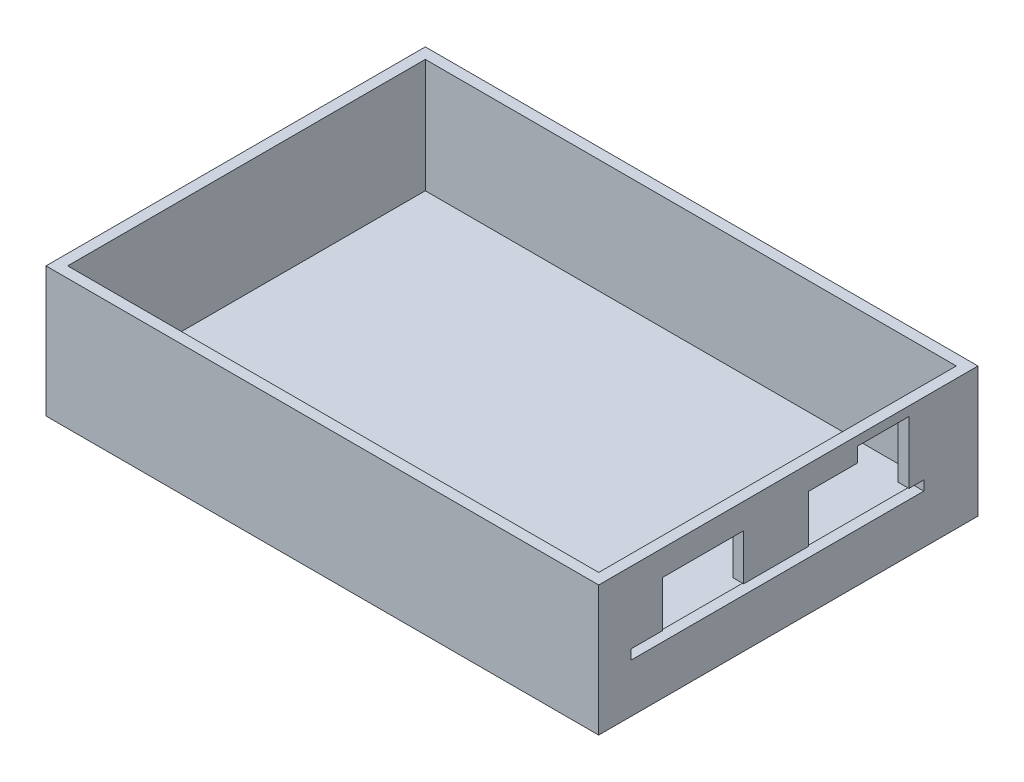
SolidWorks part; units mm, degrees
ref_plane "Alzado" through (0, 0, 0) normal (0, 0, 1) x (1, 0, 0)
ref_plane "Planta" through (0, 0, 0) normal (0, 1, 0) x (1, 0, 0)
ref_plane "Vista lateral" through (0, 0, 0) normal (1, 0, 0) x (0, 0, -1)
sketch "Croquis1" plane through (0, 0, 0) normal (0, 1, 0) x (1, 0, 0)
  line L1 (0, 0) -> (102, 0)
  line L2 (0, 0) -> (0, 70)
  line L3 (0, 70) -> (102, 70)
  line L4 (102, 0) -> (102, 70)
  dimension "D1" = 70
  dimension "D2" = 102
extrude "Saliente-Extruir1" add sketch "Croquis1" along normal blind 24
sketch "Croquis2" plane through (0, 24, 0) normal (0, 1, 0) x (1, 0, 0)
  line L0 (0, 70) -> (0, 0) construction
  line L1 (2, 2) -> (100, 2)
  line L2 (2, 2) -> (2, 68)
  line L3 (2, 68) -> (100, 68)
  line L4 (100, 2) -> (100, 68)
  line L5 (0, 0) -> (102, 0) construction
  line L6 (102, 0) -> (102, 70) construction
  line L7 (102, 70) -> (0, 70) construction
  dimension "D1" = 2
  dimension "D2" = 2
  dimension "D3" = 2
  dimension "D4" = 2
extrude "Cortar-Extruir1" cut sketch "Croquis2" against normal offset from surface (21 mm away) 3 up to face at (51, 0, -35)
sketch "Croquis3" plane through (102, 0, 0) normal (1, 0, 0) x (0, 0, -1)
  line L0 (0, 9) -> (70, 9) construction
  line L1 (0, 24) -> (0, 0) construction
  line L2 (70, 24) -> (70, 0) construction
  line L3 (0, 0) -> (70, 0) construction
  line L4 (6, 9) -> (60, 9)
  line L5 (60, 9) -> (60, 10.8)
  line L6 (60, 10.8) -> (57.25, 10.8)
  line L7 (57.25, 10.8) -> (57.25, 22.3)
  line L8 (57.25, 22.3) -> (47.75, 22.3)
  line L9 (47.75, 22.3) -> (47.75, 19.6)
  line L10 (47.75, 19.6) -> (38.75, 19.6)
  line L11 (38.75, 19.6) -> (38.75, 10.8)
  line L12 (38.75, 10.8) -> (26.75, 10.8)
  line L13 (26.75, 10.8) -> (26.75, 19.3)
  line L14 (26.75, 19.3) -> (11.75, 19.3)
  line L15 (11.75, 19.3) -> (11.75, 10.8)
  line L16 (11.75, 10.8) -> (6, 10.8)
  line L17 (6, 10.8) -> (6, 9)
  line L18 (38.75, 10.8) -> (38.75, 9) construction
  line L19 (26.75, 10.8) -> (26.75, 9) construction
  point P10 (0, 0)
  dimension "D1" = 9
  dimension "D2" = 1.8
  dimension "D3" = 11.5
  dimension "D4" = 2.75
  dimension "D5" = 10
  dimension "D6" = 9.5
  dimension "D7" = 2.7
  dimension "D8" = 9
  dimension "D9" = 8.5
  dimension "D10" = 15
  dimension "D11" = 54
  dimension "D12" = 12
extrude "Cortar-Extruir2" cut sketch "Croquis3" against normal up to surface (2 mm away) up to face at (100, 13.5, -35)
